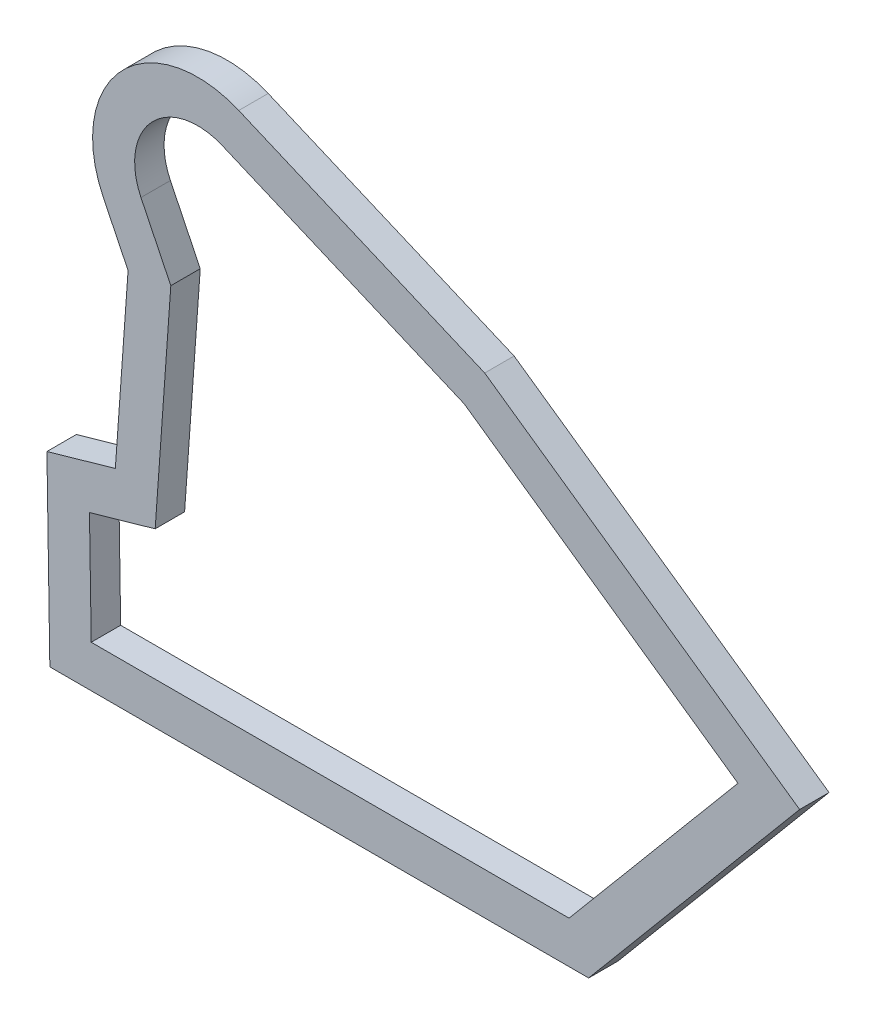
SolidWorks part; units mm, degrees
ref_plane "Front Plane" through (0, 0, 0) normal (0, 0, 1) x (1, 0, 0)
ref_plane "Top Plane" through (0, 0, 0) normal (0, 1, 0) x (1, 0, 0)
ref_plane "Right Plane" through (0, 0, 0) normal (1, 0, 0) x (0, 0, -1)
sketch "Sketch1" plane through (0, 0, 0) normal (0, 0, 1) x (1, 0, 0)
  line L1 (22.0377, 65.8411) -> (45.4373, 55.9086)
  line L4 (20.4748, 62.1591) -> (22.0377, 65.8411) construction
  line L6 (43.4874, 52.3908) -> (69.5364, 34.1511)
  line L7 (69.5364, 34.1511) -> (53.4667, 15)
  line L8 (53.4667, 15) -> (8, 15)
  line L9 (8, 15) -> (7.8329, 25.6071)
  line L10 (7.8329, 25.6071) -> (14.0841, 27.3881)
  line L11 (14.0841, 27.3881) -> (15.5726, 48.168)
  line L12 (15.5726, 48.168) -> (12.7332, 54.015)
  line L13 (43.4874, 52.3908) -> (20.4748, 62.1591)
  line L14 (45.4373, 55.9086) -> (75.4065, 34.9239)
  line L15 (75.4065, 34.9239) -> (55.332, 11)
  line L16 (55.332, 11) -> (4.0625, 11)
  line L17 (4.0625, 11) -> (3.785, 28.613)
  line L18 (3.785, 28.613) -> (10.2944, 30.4676)
  line L19 (10.2944, 30.4676) -> (11.5063, 47.3848)
  line L20 (11.5063, 47.3848) -> (9.135, 52.2676)
  line L21 (55, 0) -> (-55, 0) construction
  arc A0 (20.4748, 62.1591) -> (12.7332, 54.015) centre (18.1304, 56.6361) ccw
  arc A1 (22.0377, 65.8411) -> (9.135, 52.2676) centre (18.1304, 56.6361) ccw
  point P9 (0, 0)
  point P20 (0, 0)
  dimension "D16" = 12
  dimension "D3" = 85
  dimension "D4" = 168
  dimension "D5" = 130
  dimension "D6" = 105
  dimension "D7" = 250
  dimension "D8" = 8
  dimension "D9" = 25
  dimension "D10" = 31.8
  dimension "D11" = 15
  dimension "D12" = 6.5
  dimension "D13" = 210
  dimension "D14" = 25
  dimension "D15" = 45.4667
  dimension "D17" = 6.5
  dimension "D18" = 20.8332
  dimension "D19" = 4
  dimension "D20" = 4
  dimension "D21" = 4
  dimension "D22" = 4
  dimension "D23" = 4
  dimension "D24" = 4
  dimension "D25" = 4
extrude "Boss-Extrude1" add sketch "Sketch1" along normal blind 2.8
sketch "Sketch2" plane through (0, 0, 0) normal (0, 0, 1) x (1, 0, 0)
  line L0 (42.5112, 51.7208) -> (69.0291, 34.1699) construction
  line L1 (69.0291, 34.1699) -> (53.4667, 14.6043) construction
  line L2 (53.4667, 14.6043) -> (8, 15) construction
  line L3 (8, 15) -> (7.6106, 24) construction
  line L4 (7.6106, 24) -> (13.8106, 25.9521) construction
  line L5 (13.8106, 25.9521) -> (14.7275, 46.7651) construction
  line L6 (14.7275, 46.7651) -> (11.7285, 52.5319) construction
  line L7 (42.5112, 51.7208) -> (19.2505, 60.8828) construction
  line L8 (42.5112, 51.7208) -> (69.0291, 34.1699)
  line L9 (69.0291, 34.1699) -> (53.4667, 14.6043)
  line L10 (53.4667, 14.6043) -> (8, 15)
  line L11 (8, 15) -> (7.6106, 24)
  line L12 (7.6106, 24) -> (13.8106, 25.9521)
  line L13 (13.8106, 25.9521) -> (14.7275, 46.7651)
  line L14 (14.7275, 46.7651) -> (11.7285, 52.5319)
  line L15 (42.5112, 51.7208) -> (19.2505, 60.8828)
  arc A0 (19.2505, 60.8828) -> (11.7285, 52.5319) centre (17.0516, 55.3003) ccw construction
  arc A1 (19.2505, 60.8828) -> (11.7285, 52.5319) centre (17.0516, 55.3003) ccw
